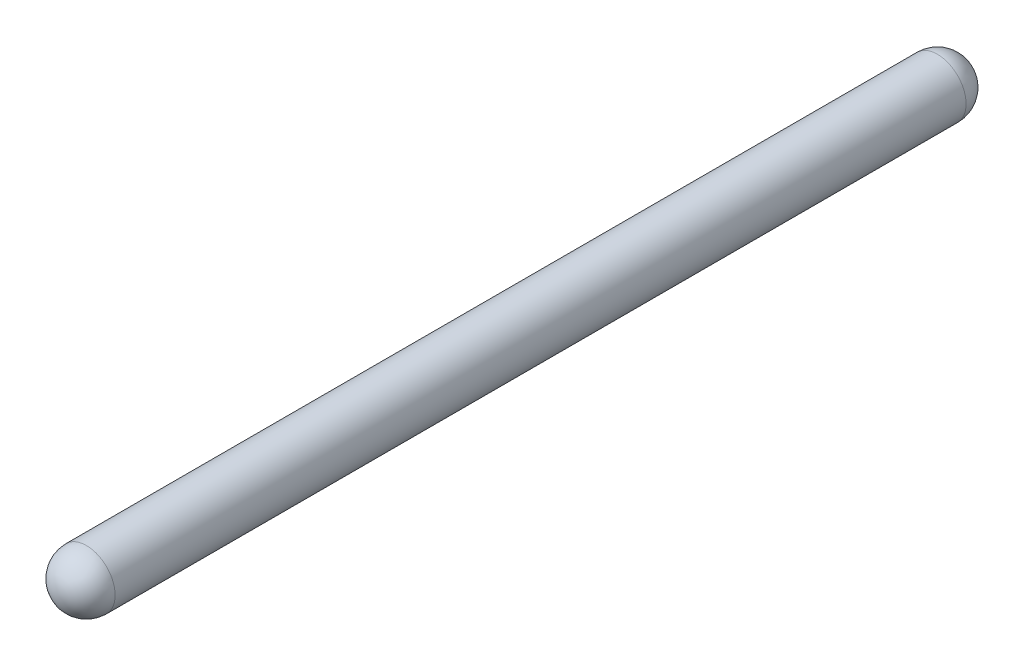
SolidWorks part; units mm, degrees
ref_plane "Front Plane" through (0, 0, 0) normal (0, 0, 1) x (1, 0, 0)
ref_plane "Top Plane" through (0, 0, 0) normal (0, 1, 0) x (1, 0, 0)
ref_plane "Right Plane" through (0, 0, 0) normal (1, 0, 0) x (0, 0, -1)
sketch "Sketch1" plane through (0, 0, 0) normal (0, 0, 1) x (1, 0, 0)
  circle A1 centre (-85.4112, 272.8722) radius 10.922
  point P3 (-85.4112, 272.8722)
extrude "Boss-Extrude1" add sketch "Sketch1" along normal mid plane 323.85
sketch "Sketch3" plane through (0, 0, -161.925) normal (0, 0, -1) x (-1, 0, 0)
  line L1 (74.4892, 272.8722) -> (96.3332, 272.8722)
  circle A2 centre (85.4112, 272.8722) radius 10.922 construction
  arc A3 (96.3332, 272.8722) -> (74.4892, 272.8722) centre (85.4112, 272.8722) ccw
revolve "Revolve2" add sketch "Sketch3" angle 360 about L1
sketch "Sketch4" plane through (0, 0, 161.925) normal (0, 0, 1) x (1, 0, 0)
  line L0 (-74.4892, 272.8722) -> (-96.3332, 272.8722)
  circle A0 centre (-85.4112, 272.8722) radius 10.922 construction
  arc A1 (-74.4892, 272.8722) -> (-96.3332, 272.8722) centre (-85.4112, 272.8722) ccw
revolve "Revolve3" add sketch "Sketch4" angle 360 about L0
